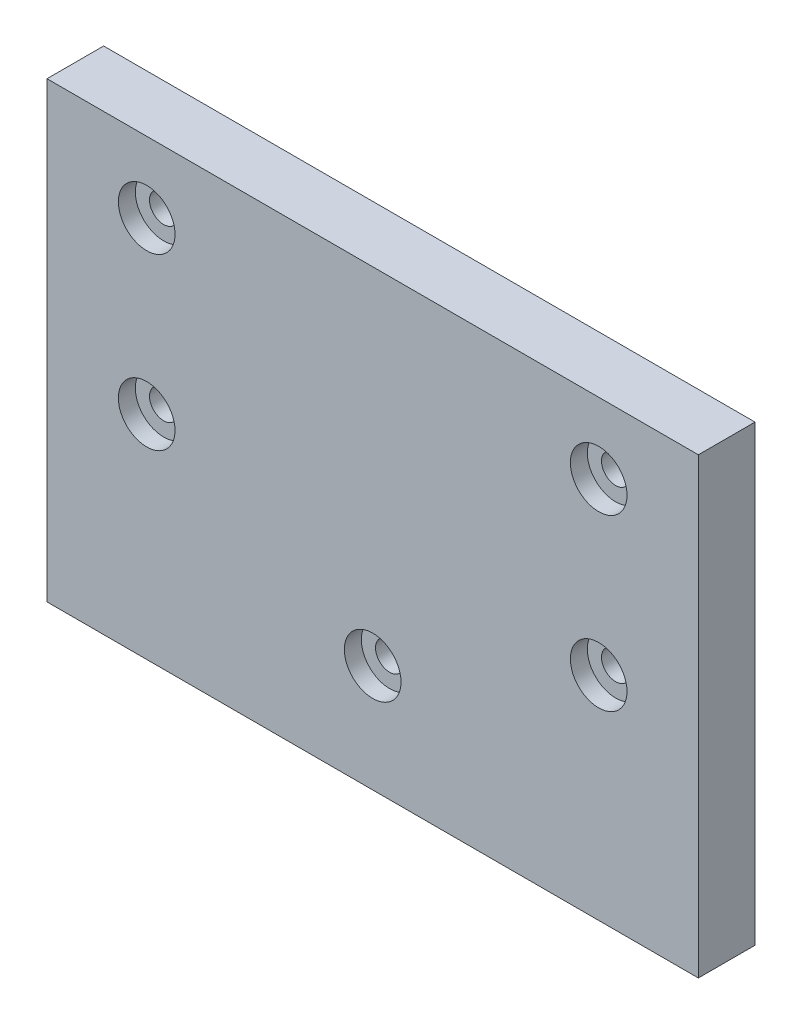
SolidWorks part; units mm, degrees
ref_plane "Front Plane" through (0, 0, 0) normal (0, 0, 1) x (1, 0, 0)
ref_plane "Top Plane" through (0, 0, 0) normal (0, 1, 0) x (1, 0, 0)
ref_plane "Right Plane" through (0, 0, 0) normal (1, 0, 0) x (0, 0, -1)
sketch "Sketch1" plane through (0, 0, 0) normal (0, 0, 1) x (1, 0, 0)
  line L1 (-57.5, 40) -> (57.5, 40)
  line L2 (-57.5, 40) -> (-57.5, -40)
  line L3 (-57.5, -40) -> (57.5, -40)
  line L4 (57.5, 40) -> (57.5, -40)
  line L5 (-57.5, 40) -> (57.5, -40) construction
  line L6 (-57.5, -40) -> (57.5, 40) construction
  point P0 (0, 0)
  dimension "D1" = 115
  dimension "D2" = 80
extrude "Boss-Extrude1" add sketch "Sketch1" along normal blind 10
sketch "Sketch2" plane through (0, 0, 10) normal (0, 0, 1) x (1, 0, 0)
  line L1 (-57.5, 40) -> (-57.5, -40) construction
  circle A0 centre (-39.9, 27.5) radius 2.5
  point P2 (0, 0)
  point P4 (0, 0)
  dimension "D1" = 5
  dimension "D2" = 27.5
  dimension "D3" = 17.6
extrude "Cut-Extrude1" cut sketch "Sketch2" against normal blind 10
pattern_linear "LPattern1" count 2 spacing 79.8 along (1, 0, 0) count 2 spacing 30 along (0, -1, 0) of "Cut-Extrude1"
sketch "Sketch4" plane through (0, 0, 10) normal (0, 0, 1) x (1, 0, 0)
  circle A0 centre (-39.9, 27.5) radius 5
  circle A1 centre (-39.9, 27.5) radius 2.5 construction
  dimension "D1" = 10
extrude "Cut-Extrude2" cut sketch "Sketch4" against normal blind 3
pattern_linear "LPattern2" count 2 spacing 79.8 along (1, 0, 0) count 2 spacing 30 along (0, -1, 0) of "Cut-Extrude2"
sketch "Sketch5" plane through (0, 0, 10) normal (0, 0, 1) x (1, 0, 0)
  circle A0 centre (0, -21.0097) radius 2.5
  dimension "D1" = 5
extrude "Cut-Extrude3" cut sketch "Sketch5" against normal through all
sketch "Sketch6" plane through (0, 0, 10) normal (0, 0, 1) x (1, 0, 0)
  circle A0 centre (0, -21.0097) radius 5
  dimension "D1" = 10
extrude "Cut-Extrude4" cut sketch "Sketch6" against normal blind 3
